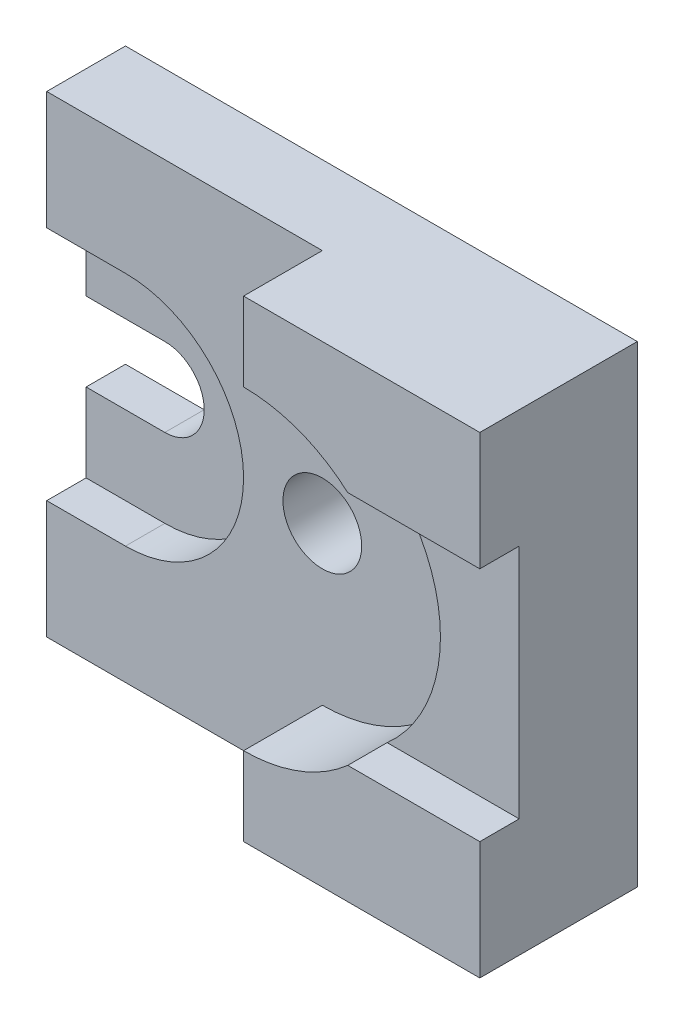
SolidWorks part; units mm, degrees
ref_plane "Front Plane" through (0, 0, 0) normal (0, 0, 1) x (1, 0, 0)
ref_plane "Top Plane" through (0, 0, 0) normal (0, 1, 0) x (1, 0, 0)
ref_plane "Right Plane" through (0, 0, 0) normal (1, 0, 0) x (0, 0, -1)
sketch "Sketch1" plane through (0, 0, 0) normal (0, 0, 1) x (1, 0, 0)
  line L1 (0, 0) -> (130, 0)
  line L2 (0, 0) -> (0, 120)
  line L3 (0, 120) -> (130, 120)
  line L4 (130, 0) -> (130, 120)
  dimension "D1" = 130
  dimension "D2" = 120
extrude "Boss-Extrude1" add sketch "Sketch1" along normal blind 40
sketch "Sketch2" plane through (0, 0, 40) normal (0, 0, 1) x (1, 0, 0)
  line L0 (0, 70) -> (20, 70)
  line L1 (0, 120) -> (0, 0) construction
  line L2 (0, 50) -> (20, 50)
  line L3 (0, 70) -> (0, 50)
  arc A0 (20, 70) -> (20, 50) centre (20, 60) cw
  dimension "D1" = 10
  dimension "D2" = 20
  dimension "D3" = 20
  dimension "D4" = 20
  dimension "D5" = 50
extrude "Cut-Extrude1" cut sketch "Sketch2" against normal blind 40
sketch "Sketch3" plane through (0, 0, 40) normal (0, 0, 1) x (1, 0, 0)
  line L0 (0, 90) -> (20, 90)
  line L1 (0, 120) -> (0, 70) construction
  line L2 (0, 30) -> (20, 30)
  line L3 (0, 50) -> (0, 0) construction
  line L4 (0, 90) -> (0, 70)
  line L5 (0, 70) -> (20, 70)
  line L6 (0, 30) -> (0, 50)
  line L7 (0, 50) -> (20, 50)
  line L8 (0, 70) -> (0, 90)
  arc A0 (20, 90) -> (20, 30) centre (20, 60) cw
  arc A1 (20, 70) -> (20, 50) centre (20, 60) cw
  line M1 (0, 120) -> (0, 70)
  line M2 (0, 70) -> (20, 70)
  arc M3 (20, 70) -> (20, 50) centre (20, 60) cw
  line M4 (20, 50) -> (0, 50)
  line M5 (0, 50) -> (0, 0)
  dimension "D3" = 30
  dimension "D1" = 20
  dimension "D2" = 20
  dimension "D4" = 0
extrude "Cut-Extrude2" cut sketch "Sketch3" against normal blind 10 contours A0 L0 L2 M1 M2 M3 M4 M5
sketch "Sketch4" plane through (0, 0, 40) normal (0, 0, 1) x (1, 0, 0)
  line L0 (130, 120) -> (0, 120) construction
  circle A0 centre (70, 60) radius 10
  arc A1 (20, 50) -> (20, 70) centre (20, 60) ccw construction
  point P2 (30, 60)
  dimension "D1" = 20
  dimension "D2" = 40
  dimension "D3" = 60
extrude "Cut-Extrude4" cut sketch "Sketch4" against normal blind 159
sketch "Sketch6" plane through (0, 0, 30) normal (0, 0, 1) x (1, 0, 0)
  line L0 (0, 90) -> (20, 90)
  line L1 (0, 30) -> (20, 30)
  line L2 (0, 30) -> (20, 30) construction
  line L3 (0, 30) -> (0, 50)
  line L4 (0, 50) -> (20, 50)
  line L5 (20, 70) -> (0, 70)
  line L6 (0, 70) -> (0, 90)
  arc A0 (20, 30) -> (20, 90) centre (20, 60) ccw construction
  arc A1 (20, 70) -> (20, 50) centre (20, 60) cw
  arc A2 (20, 50) -> (20, 70) centre (20, 60) ccw construction
  arc A3 (20, 90) -> (20, 30) centre (20, 60) cw
  dimension "D1" = 30
extrude "Cut-Extrude5" cut sketch "Sketch6" against normal blind 20
sketch "Sketch7" plane through (0, 0, 40) normal (0, 0, 1) x (1, 0, 0)
  line L0 (0, 90) -> (0, 120)
  line L1 (0, 120) -> (70, 120)
  line L2 (130, 120) -> (0, 120) construction
  line L3 (70, 120) -> (70, 100)
  line L4 (70, 0) -> (70, 20)
  line L5 (0, 0) -> (130, 0) construction
  line L6 (70, 0) -> (0, 0)
  line L7 (0, 0) -> (0, 30)
  line L8 (0, 30) -> (20, 30)
  line L9 (0, 90) -> (20, 90)
  arc A0 (70, 100) -> (70, 20) centre (70, 60) cw
  arc A1 (20, 90) -> (20, 30) centre (20, 60) cw
  circle A2 centre (70, 60) radius 10
  circle M13 centre (70, 60) radius 10
  arc M14 (20, 90) -> (20, 30) centre (20, 60) cw
  line M15 (20, 30) -> (0, 30)
  line M16 (0, 30) -> (0, 0)
  line M17 (0, 0) -> (130, 0)
  line M19 (130, 120) -> (0, 120)
  line M20 (0, 120) -> (0, 90)
  line M21 (0, 90) -> (20, 90)
  dimension "D2" = 40
  dimension "D4" = 20
  dimension "D1" = 70
  dimension "D3" = 0
extrude "Cut-Extrude6" cut sketch "Sketch7" against normal blind 20 contours A0 L3 L4 M19 M20 M21 M14 M15 M16 M17 M13
sketch "Sketch8" plane through (0, 0, 40) normal (0, 0, 1) x (1, 0, 0)
  line L0 (96.4575, 90) -> (130, 90)
  line L1 (130, 0) -> (130, 120) construction
  line L2 (130, 90) -> (130, 30)
  line L3 (130, 30) -> (96.4575, 30)
  arc A0 (70, 20) -> (70, 100) centre (70, 60) ccw construction
  arc A1 (96.4575, 90) -> (96.4575, 30) centre (70, 60) cw
  dimension "D1" = 30
  dimension "D2" = 30
extrude "Cut-Extrude7" cut sketch "Sketch8" against normal blind 10
